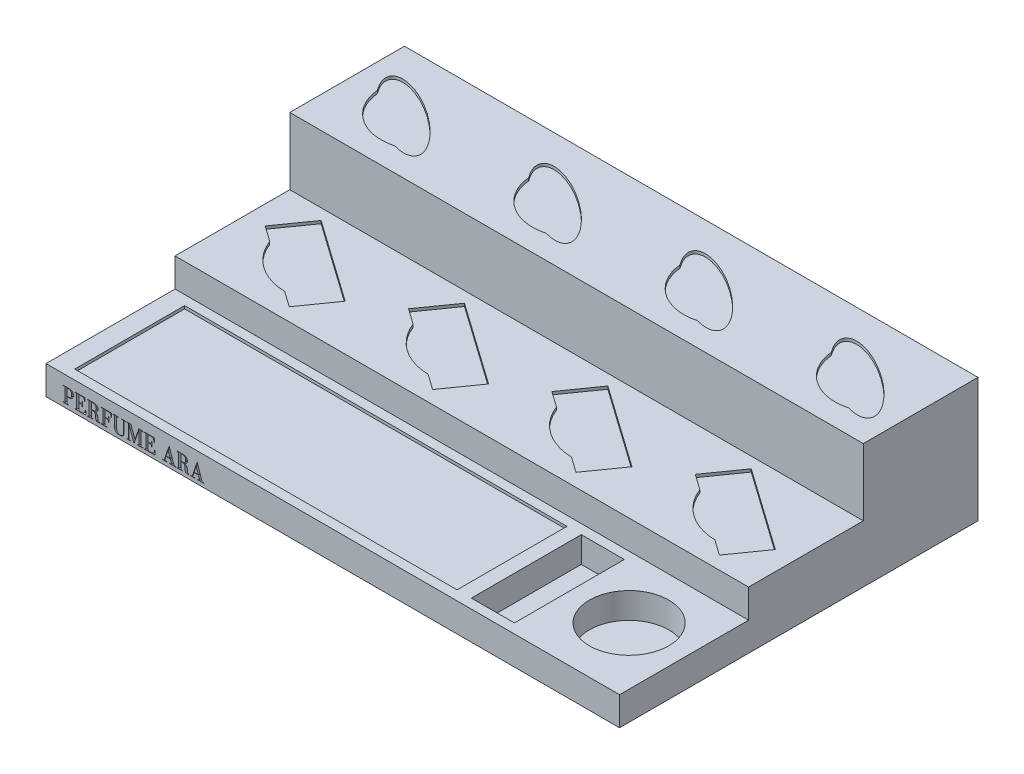
SolidWorks part; units mm, degrees
ref_plane "Front Plane" through (0, 0, 0) normal (0, 0, 1) x (1, 0, 0)
ref_plane "Top Plane" through (0, 0, 0) normal (0, 1, 0) x (1, 0, 0)
ref_plane "Right Plane" through (0, 0, 0) normal (1, 0, 0) x (0, 0, -1)
sketch "Sketch2" plane through (0, 0, 0) normal (1, 0, 0) x (0, 0, -1)
  line L0 (0, 0) -> (375, 0)
  line L1 (375, 0) -> (375, 130)
  line L2 (375, 130) -> (255, 130)
  line L3 (255, 130) -> (255, 60)
  line L4 (255, 60) -> (135, 60)
  line L7 (0, 0) -> (0, 30)
  line L9 (0, 30) -> (135, 30)
  line L10 (135, 30) -> (135, 60)
  point P7 (135, 60)
  dimension "D1" = 70
  dimension "D2" = 30
  dimension "D3" = 375
  dimension "D4" = 120
  dimension "D5" = 120
  dimension "D6" = 60
extrude "Boss-Extrude2" add sketch "Sketch2" along normal blind 600
sketch "Sketch4" plane through (0, 60, 0) normal (0, 1, 0) x (1, 0, 0)
  line L0 (20, 209.2488) -> (44.2237, 243.5593)
  line L1 (20, 209.2488) -> (36.3383, 197.7137)
  line L2 (44.2237, 243.5593) -> (130, 183)
  line L3 (105.7763, 148.6895) -> (130, 183)
  line L4 (600, 255) -> (0, 255) construction
  line L6 (89.4379, 160.2246) -> (105.7763, 148.6895)
  line L7 (170, 209.2488) -> (194.2237, 243.5593)
  line L8 (194.2237, 243.5593) -> (280, 183)
  line L9 (255.7763, 148.6895) -> (280, 183)
  line L10 (239.4379, 160.2246) -> (255.7763, 148.6895)
  line L12 (170, 209.2488) -> (186.3383, 197.7137)
  line L14 (0, 255) -> (0, 135) construction
  line L15 (320, 209.2488) -> (344.2237, 243.5593)
  line L16 (344.2237, 243.5593) -> (430, 183)
  line L17 (405.7763, 148.6895) -> (430, 183)
  line L18 (389.4379, 160.2246) -> (405.7763, 148.6895)
  line L19 (320, 209.2488) -> (336.3383, 197.7137)
  line L20 (470, 209.2488) -> (494.2237, 243.5593)
  line L21 (494.2237, 243.5593) -> (580, 183)
  line L22 (555.7763, 148.6895) -> (580, 183)
  line L23 (539.4379, 160.2246) -> (555.7763, 148.6895)
  line L24 (470, 209.2488) -> (486.3383, 197.7137)
  line L25 (600, 255) -> (600, 135) construction
  arc A0 (36.3383, 197.7137) -> (89.4379, 160.2246) centre (90.4643, 218.028) ccw
  arc A1 (186.3383, 197.7137) -> (239.4379, 160.2246) centre (240.4643, 218.028) ccw
  arc A2 (336.3383, 197.7137) -> (389.4379, 160.2246) centre (390.4643, 218.028) ccw
  arc A3 (486.3383, 197.7137) -> (539.4379, 160.2246) centre (540.4643, 218.028) ccw
  point P7 (57.1206, 170.8)
  dimension "D8" = 10
  dimension "D2" = 105
  dimension "D3" = 42
  dimension "D4" = 150
  dimension "D5" = 20
  dimension "D6" = 20
  dimension "D7" = 20
  dimension "D9" = 4
  dimension "D10" = 20
  dimension "D11" = 72
sketch "Sketch9" plane through (0, 130, 0) normal (0, 1, 0) x (1, 0, 0)
  line L0 (62.5959, 311.1223) -> (105.1918, 281.2963) construction
  line L1 (105.1918, 281.2963) -> (-8.1153, 281.2963) construction
  line L2 (600, 375) -> (600, 255) construction
  line L3 (0, 375) -> (0, 255) construction
  line L4 (600, 375) -> (0, 375) construction
  arc A0 (25.7928, 320.9482) -> (85.1918, 279.6701) centre (72.6507, 325) ccw
  arc A1 (184.0622, 320.9482) -> (243.4612, 279.6701) centre (230.9201, 325) ccw
  arc A2 (342.3316, 320.9482) -> (401.7306, 279.6701) centre (389.1895, 325) ccw
  arc A3 (500.601, 320.9482) -> (560, 279.6701) centre (547.4589, 325) ccw
  ellipse E0 centre (62.5959, 311.1223) end of major axis (20, 340.9482) minor radius 18 (85.1918, 279.6701) -> (25.7928, 320.9482) ccw
  ellipse E1 centre (220.8653, 311.1223) end of major axis (263.4612, 281.2963) minor radius 18 (243.4612, 279.6701) -> (184.0622, 320.9482) ccw
  ellipse E2 centre (379.1347, 311.1223) end of major axis (421.7306, 281.2963) minor radius 18 (401.7306, 279.6701) -> (342.3316, 320.9482) ccw
  ellipse E3 centre (537.4041, 311.1223) end of major axis (494.8082, 340.9482) minor radius 18 (560, 279.6701) -> (500.601, 320.9482) ccw
  point P10 (45.8108, 286.3775)
  dimension "D1" = 104
  dimension "D2" = 36
  dimension "D3" = 20
  dimension "D4" = 35
  dimension "D5" = 20
  dimension "D6" = 20
  dimension "D7" = 10
  dimension "D9" = 20
  dimension "D10" = 50
  dimension "D8" = 4
extrude "Cut-Extrude3" cut sketch "Sketch9" against normal blind 3
extrude "Cut-Extrude4" cut sketch "Sketch4" against normal blind 3
sketch "Sketch11" plane through (0, 0, 0) normal (0, 0, 1) x (1, 0, 0)
  line L0 (0, 30) -> (0, 0) construction
  text T0 "PERFUME ARA" font "BodoniFLF" height in points 50
  dimension "D1" = 17
extrude "Cut-Extrude6" cut sketch "Sketch11" against normal blind 3
sketch "Sketch12" plane through (0, 30, 0) normal (0, 1, 0) x (1, 0, 0)
  line L1 (20, 125) -> (420, 125)
  line L2 (20, 125) -> (20, 10)
  line L3 (20, 10) -> (420, 10)
  line L4 (420, 125) -> (420, 10)
  line L5 (600, 135) -> (0, 135) construction
  line L6 (600, 0) -> (0, 0) construction
  point P4 (0, 0)
  dimension "D1" = 10
  dimension "D2" = 10
  dimension "D3" = 400
extrude "Cut-Extrude7" cut sketch "Sketch12" against normal blind 3
sketch "Sketch13" plane through (0, 30, 0) normal (0, 1, 0) x (1, 0, 0)
  line L0 (420, 10) -> (420, 125) construction
  line L1 (435, 125) -> (480, 125)
  line L2 (435, 125) -> (435, 10)
  line L3 (435, 10) -> (480, 10)
  line L4 (480, 125) -> (480, 10)
  line L6 (600, 0) -> (0, 0) construction
  line L7 (600, 135) -> (600, 0) construction
  circle A0 centre (540, 70) radius 41.5
  dimension "D3" = 83
  dimension "D4" = 70
  dimension "D5" = 60
  dimension "D1" = 15
  dimension "D2" = 45
extrude "Cut-Extrude9" cut sketch "Sketch13" against normal offset from surface (27 mm away) 3 up to face at (300, 0, -187.5)
